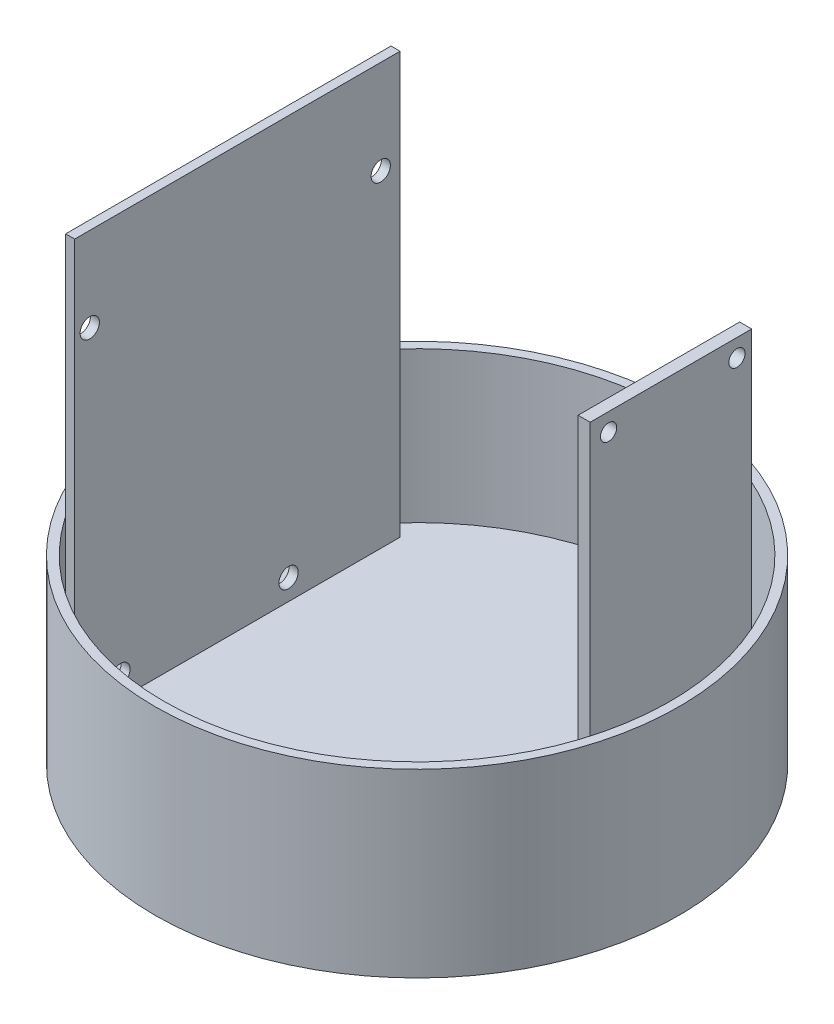
SolidWorks part; units mm, degrees
ref_plane "Front Plane" through (0, 0, 0) normal (0, 0, 1) x (1, 0, 0)
ref_plane "Top Plane" through (0, 0, 0) normal (0, 1, 0) x (1, 0, 0)
ref_plane "Right Plane" through (0, 0, 0) normal (1, 0, 0) x (0, 0, -1)
sketch "Sketch1" plane through (0, 0, 0) normal (0, 1, 0) x (1, 0, 0)
  circle A0 centre (0, 0) radius 43.5
  dimension "D1" = 87
extrude "Boss-Extrude1" add sketch "Sketch1" along normal blind 30
sketch "Sketch2" plane through (0, 30, 0) normal (0, 1, 0) x (1, 0, 0)
  circle A0 centre (0, 0) radius 42
  dimension "D1" = 84
extrude "Cut-Extrude1" cut sketch "Sketch2" along normal through all and the other way blind 25
sketch "Sketch6" plane through (0, 5, 0) normal (0, 1, 0) x (1, 0, 0)
  line L1 (-30.505, 26.1799) -> (-29.005, 26.1799)
  line L2 (-30.505, 26.1799) -> (-30.505, -27.8201)
  line L3 (-30.505, -27.8201) -> (-29.005, -27.8201)
  line L4 (-29.005, 26.1799) -> (-29.005, -27.8201)
  dimension "D1" = 54
  dimension "D2" = 1.5
extrude "Boss-Extrude4" add sketch "Sketch6" along normal blind 80
sketch "Sketch7" plane through (-29.005, 0, 0) normal (1, 0, 0) x (0, 0, -1)
  line L0 (26.1799, 85) -> (26.1799, 5) construction
  line L1 (-27.8201, 85) -> (26.1799, 85)
  line L2 (-27.8201, 85) -> (-27.8201, 78.7313)
  line L3 (-27.8201, 78.7313) -> (26.1799, 78.7313)
  line L4 (26.1799, 85) -> (26.1799, 78.7313)
extrude "Cut-Extrude2" cut sketch "Sketch7" against normal through all
sketch "Sketch8" plane through (-29.005, 0, 0) normal (1, 0, 0) x (0, 0, -1)
  line L0 (26.1799, 78.7313) -> (26.1799, 5) construction
  line L1 (-27.8201, 78.7313) -> (26.1799, 78.7313)
  line L2 (-27.8201, 78.7313) -> (-27.8201, 74.8607)
  line L3 (-27.8201, 74.8607) -> (26.1799, 74.8607)
  line L4 (26.1799, 78.7313) -> (26.1799, 74.8607)
extrude "Cut-Extrude3" cut sketch "Sketch8" against normal through all
sketch "Sketch9" plane through (-29.005, 0, 0) normal (1, 0, 0) x (0, 0, -1)
  circle A0 centre (-25.3201, 60.8607) radius 1.6
  circle A1 centre (22.9799, 59.2607) radius 1.6
  circle A2 centre (7.6799, 8.4607) radius 1.6
  circle A3 centre (-20.2201, 8.4607) radius 1.6
extrude "Cut-Extrude5" cut sketch "Sketch9" against normal up to next
sketch "Sketch10" plane through (0, 5, 0) normal (0, 1, 0) x (1, 0, 0)
  line L1 (30.9383, 24.6003) -> (28.9383, 24.6003)
  line L2 (30.9383, 24.6003) -> (30.9383, -4.3904)
  line L3 (30.9383, -4.3904) -> (28.9383, -4.3904)
  line L4 (28.9383, 24.6003) -> (28.9383, -4.3904)
  dimension "D1" = 2
extrude "Boss-Extrude5" add sketch "Sketch10" along normal blind 67
sketch "Sketch11" plane through (28.9383, 0, 0) normal (-1, 0, 0) x (0, 0, 1)
  line L0 (4.3904, 72) -> (4.3904, 5) construction
  line L1 (-24.6003, 72) -> (4.3904, 72)
  line L2 (-24.6003, 72) -> (-24.6003, 65.7019)
  line L3 (-24.6003, 65.7019) -> (4.3904, 65.7019)
  line L4 (4.3904, 72) -> (4.3904, 65.7019)
extrude "Cut-Extrude6" cut sketch "Sketch11" against normal up to next
sketch "Sketch12" plane through (28.9383, 0, 0) normal (-1, 0, 0) x (0, 0, 1)
  line L0 (-24.6003, 65.7019) -> (4.3904, 65.7019) construction
  line L1 (4.3904, 5) -> (2.2066, 5)
  line L2 (4.3904, 5) -> (4.3904, 65.7019)
  line L3 (4.3904, 65.7019) -> (2.2066, 65.7019)
  line L4 (2.2066, 5) -> (2.2066, 65.7019)
extrude "Cut-Extrude7" cut sketch "Sketch12" against normal up to next
sketch "Sketch13" plane through (28.9383, 0, 0) normal (-1, 0, 0) x (0, 0, 1)
  circle A0 centre (-22.1503, 62.75) radius 1.35
  circle A1 centre (-0.8503, 62.75) radius 1.35
  circle A2 centre (-22.1503, 7.45) radius 1.35
  circle A3 centre (-0.8503, 7.45) radius 1.35
extrude "Cut-Extrude8" cut sketch "Sketch13" against normal up to next
